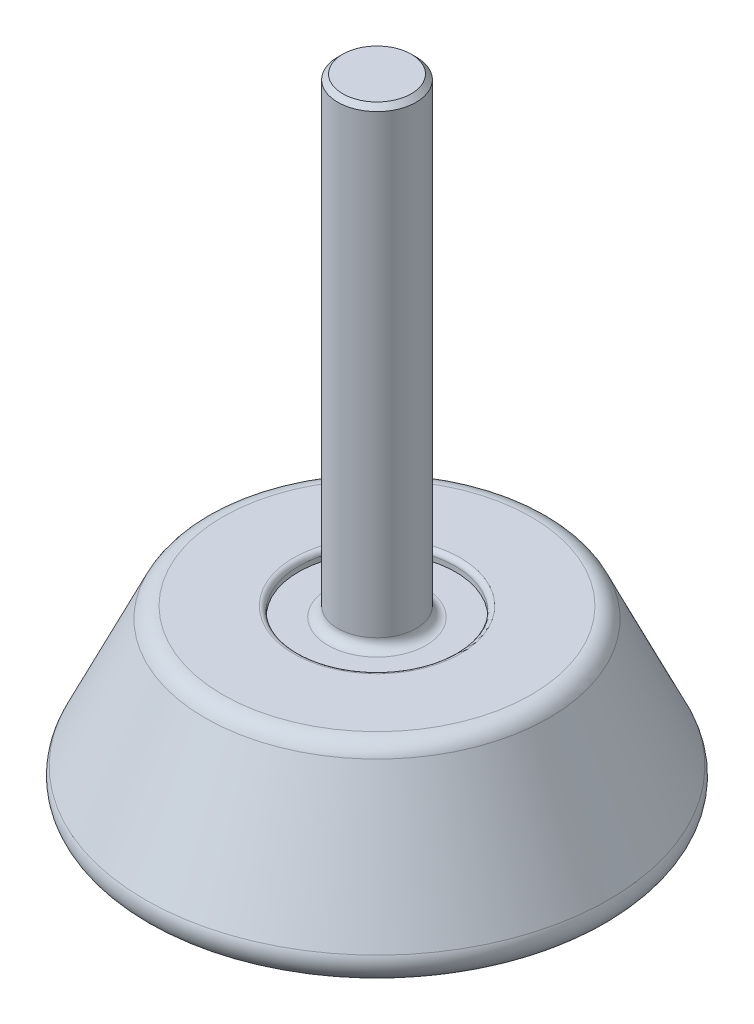
SolidWorks part; units mm, degrees
ref_plane "Alzado" through (0, 0, 0) normal (0, 0, 1) x (1, 0, 0)
ref_plane "Planta" through (0, 0, 0) normal (0, 1, 0) x (1, 0, 0)
ref_plane "Vista lateral" through (0, 0, 0) normal (1, 0, 0) x (0, 0, -1)
sketch "Croquis2" plane through (0, 0, 0) normal (0, 0, 1) x (1, 0, 0)
  line L0 (0, 0) -> (25, 0)
  line L1 (55, 0) -> (-55, 0) construction
  line L2 (25, 0) -> (17, 17)
  line L3 (17, 17) -> (8, 17)
  line L4 (8, 17) -> (8, 16)
  line L5 (8, 16) -> (4, 16)
  line L6 (4, 16) -> (4, 64)
  line L7 (4, 64) -> (0, 64)
  line L8 (0, -55) -> (0, 55) construction
  line L9 (0, 64) -> (0, 0)
  dimension "D1" = 25
  dimension "D2" = 4
  dimension "D3" = 8
  dimension "D4" = 16
  dimension "D5" = 17
  dimension "D6" = 17
  dimension "D7" = 64
revolve "Revolución1" add sketch "Croquis2" angle 360 about L9
cosmetic thread "Rosca cosmética1" parameters "D2"=6.619
fillet "Redondeo1" radius 2 2 edges at (0, 17, 17) (0, 0, 25)
fillet "Redondeo2" radius 1 1 edges at (0, 16, 4)
fillet "Redondeo3" radius 0.5 1 edges at (0, 17, 8)
chamfer "Chaflán1" distance 0.5 angle 45 1 edges at (0, 64, 4)
